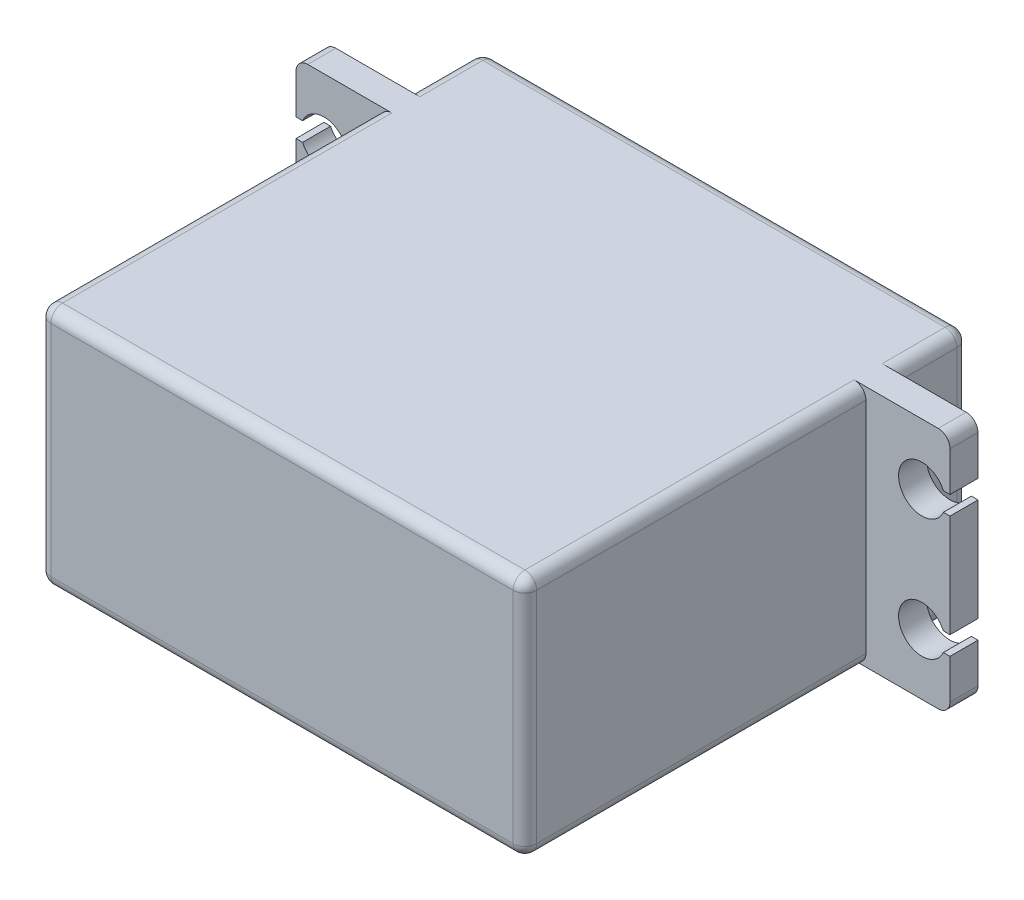
SolidWorks part; units mm, degrees
ref_plane "Front Plane" through (0, 0, 0) normal (0, 0, 1) x (1, 0, 0)
ref_plane "Top Plane" through (0, 0, 0) normal (0, 1, 0) x (1, 0, 0)
ref_plane "Right Plane" through (0, 0, 0) normal (1, 0, 0) x (0, 0, -1)
sketch "Sketch1" plane through (0, 0, 0) normal (0, 1, 0) x (1, 0, 0)
  line L0 (-41.275, 28.9719) -> (0, 28.9719) construction
  line L1 (0, 0) -> (-41.275, 0)
  line L2 (0, 0) -> (0, 28.9719)
  line L3 (0, 37.7031) -> (-41.275, 37.7031)
  line L4 (-41.275, 0) -> (-41.275, 28.9719)
  line L5 (-20.6375, 37.7031) -> (-20.6375, 0) construction
  line L6 (0, 28.9719) -> (7.1437, 28.9719)
  line L7 (-41.275, 31.3531) -> (-48.4187, 31.3531)
  line L8 (0, 31.3531) -> (0, 37.7031)
  line L9 (-41.275, 28.9719) -> (-48.4187, 28.9719)
  line L10 (-48.4187, 31.3531) -> (-48.4187, 28.9719)
  line L11 (7.1437, 31.3531) -> (7.1437, 28.9719)
  line L12 (0, 31.3531) -> (7.1437, 31.3531)
  line L13 (-41.275, 31.3531) -> (-41.275, 37.7031)
  dimension "D1" = 41.275
  dimension "D2" = 37.7031
  dimension "D3" = 28.9719
  dimension "D4" = 7.1437
  dimension "D5" = 2.3813
extrude "Boss-Extrude1" add sketch "Sketch1" along normal blind 20.6375
sketch "Sketch2" plane through (0, 0, -31.3531) normal (0, 0, -1) x (-1, 0, 0)
  line L0 (-7.1437, 10.3187) -> (48.4187, 10.3187) construction
  line L1 (-7.1437, 20.6375) -> (-7.1437, 0) construction
  line L2 (48.4187, 20.6375) -> (48.4187, 0) construction
  line L3 (0, 20.6375) -> (0, 0) construction
  line L4 (20.6375, 20.6375) -> (20.6375, 0) construction
  line L5 (0, 20.6375) -> (41.275, 20.6375) construction
  line L6 (0, 0) -> (41.275, 0) construction
  line L7 (-4.7625, 15.4781) -> (46.0375, 15.4781) construction
  line L8 (-7.1437, 16.2719) -> (-6.5812, 16.2719)
  line L9 (-7.1437, 14.6844) -> (-6.5812, 14.6844)
  line L10 (47.8562, 16.2719) -> (48.4187, 16.2719)
  line L11 (47.8562, 14.6844) -> (48.4187, 14.6844)
  line L12 (48.4187, 14.6844) -> (48.4187, 16.2719)
  line L13 (-7.1437, 14.6844) -> (-7.1437, 16.2719)
  line L14 (47.8562, 4.3656) -> (48.4187, 4.3656)
  line L15 (48.4187, 5.9531) -> (48.4187, 4.3656)
  line L16 (47.8562, 5.9531) -> (48.4187, 5.9531)
  line L17 (-7.1437, 5.9531) -> (-6.5812, 5.9531)
  line L18 (-7.1437, 5.9531) -> (-7.1437, 4.3656)
  line L19 (-7.1437, 4.3656) -> (-6.5812, 4.3656)
  arc A0 (-6.5812, 14.6844) -> (-6.5812, 16.2719) centre (-4.7625, 15.4781) ccw
  arc A1 (-6.5812, 5.9531) -> (-6.5812, 4.3656) centre (-4.7625, 5.1594) cw
  arc A2 (47.8562, 14.6844) -> (47.8562, 16.2719) centre (46.0375, 15.4781) cw
  arc A3 (47.8562, 5.9531) -> (47.8562, 4.3656) centre (46.0375, 5.1594) ccw
  dimension "D1" = 3.9688
  dimension "D2" = 5.1594
  dimension "D3" = 4.7625
  dimension "D4" = 0.7937
extrude "Cut-Extrude1" cut sketch "Sketch2" against normal through all
fillet "Fillet1" radius 1 4 edges at (-48.4187, 20.6375, -30.1625) (-48.4187, 0, -30.1625) (7.1437, 0, -30.1625) (7.1437, 20.6375, -30.1625)
fillet "Fillet2" radius 1 16 edges at (-20.6375, 0, -37.7031) (-20.6375, 20.6375, -37.7031) (-41.275, 10.3187, -37.7031) (0, 10.3187, -37.7031) (-41.275, 0, -34.5281) (-41.275, 20.6375, -34.5281) (0, 0, -34.5281) (0, 20.6375, -34.5281) (0, 0, -14.4859) (0, 20.6375, -14.4859) (0, 10.3187, 0) (-20.6375, 20.6375, 0) (-20.6375, 0, 0) (-41.275, 10.3187, 0) (-41.275, 20.6375, -14.4859) (-41.275, 0, -14.4859)
sketch "Sketch3" plane through (0, 0, -37.7031) normal (0, 0, -1) x (-1, 0, 0)
  line L0 (1, 10.3187) -> (40.275, 10.3187) construction
  line L1 (1, 19.6375) -> (1, 1) construction
  line L2 (40.275, 1) -> (40.275, 19.6375) construction
  circle A0 centre (10.2869, 10.3187) radius 4.7625
  dimension "D1" = 9.525
  dimension "D2" = 9.2869
extrude "Boss-Extrude2" add sketch "Sketch3" along normal blind 1.5875
fillet "Fillet3" radius 1 1 edges at (-5.5244, 10.3187, -37.7031)
sketch "Sketch4" plane through (0, 0, -39.2906) normal (0, 0, -1) x (-1, 0, 0)
  circle A0 centre (10.2869, 10.3187) radius 3.9688
  dimension "D1" = 7.9375
extrude "Boss-Extrude3" add sketch "Sketch4" along normal blind 1.5875
